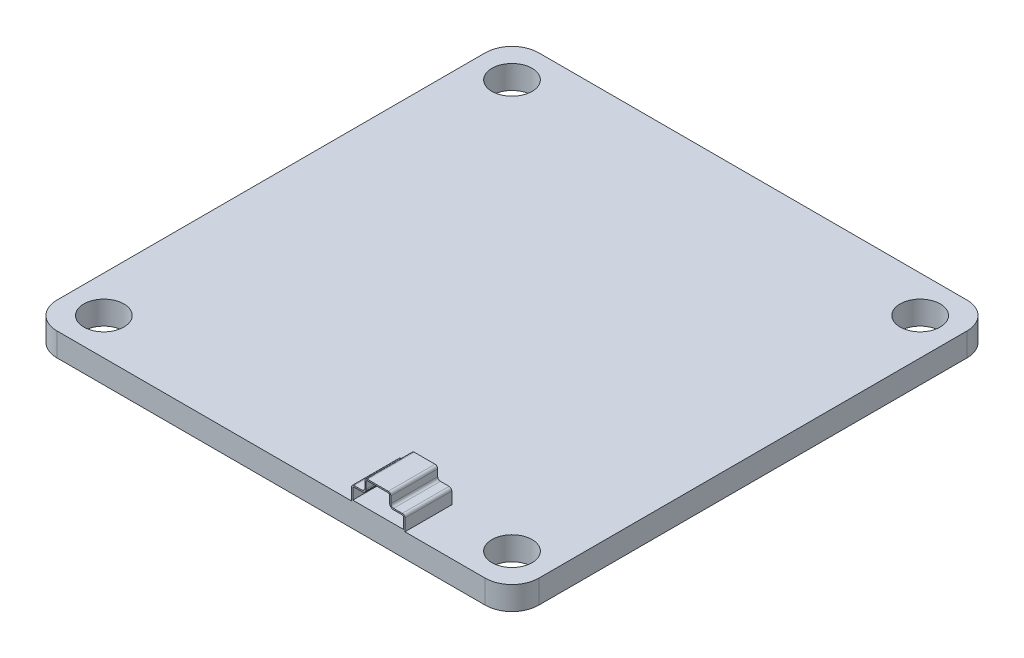
SolidWorks part; units mm, degrees
ref_plane "Front Plane" through (0, 0, 0) normal (0, 0, 1) x (1, 0, 0)
ref_plane "Top Plane" through (0, 0, 0) normal (0, 1, 0) x (1, 0, 0)
ref_plane "Right Plane" through (0, 0, 0) normal (1, 0, 0) x (0, 0, -1)
sketch "Sketch1" plane through (0, 0, 0) normal (0, 1, 0) x (1, 0, 0)
  line L1 (-16, 18) -> (16, 18)
  line L2 (-18, 16) -> (-18, -16)
  line L3 (-16, -18) -> (16, -18)
  line L4 (18, 16) -> (18, -16)
  line L5 (-18, 18) -> (18, -18) construction
  line L6 (-18, -18) -> (18, 18) construction
  line L7 (-15.25, 15.25) -> (15.25, 15.25) construction
  line L8 (-15.25, 15.25) -> (-15.25, -15.25) construction
  line L9 (-15.25, -15.25) -> (15.25, -15.25) construction
  line L10 (15.25, 15.25) -> (15.25, -15.25) construction
  line L11 (-15.25, 15.25) -> (15.25, -15.25) construction
  line L12 (-15.25, -15.25) -> (15.25, 15.25) construction
  circle A0 centre (-15.25, 15.25) radius 1.5
  circle A1 centre (15.25, 15.25) radius 1.5
  circle A2 centre (15.25, -15.25) radius 1.5
  circle A3 centre (-15.25, -15.25) radius 1.5
  arc A4 (-18, -16) -> (-16, -18) centre (-16, -16) ccw
  arc A5 (16, -18) -> (18, -16) centre (16, -16) ccw
  arc A6 (16, 18) -> (18, 16) centre (16, 16) cw
  arc A7 (-16, 18) -> (-18, 16) centre (-16, 16) ccw
  point P0 (0, 0)
  point P6 (0, 0)
  dimension "D3" = 3
  dimension "D4" = 2
  dimension "D1" = 36
  dimension "D2" = 30.5
extrude "Boss-Extrude2" add sketch "Sketch1" along normal blind 1.75
sketch "Sketch3" plane through (0, 0, 18) normal (0, 0, 1) x (1, 0, 0)
  line L0 (-16, 1.75) -> (16, 1.75) construction
  line L1 (6, 1.75) -> (10, 1.75)
  line L2 (6, 1.75) -> (6, 2.6439)
  line L3 (7.2024, 3.75) -> (8.7485, 3.75)
  line L4 (10, 1.75) -> (10, 2.6439)
  line L5 (16, 1.75) -> (16, 0) construction
  line L6 (7.0024, 3.55) -> (7.0024, 3.0439)
  line L7 (6.8024, 2.8439) -> (6.2, 2.8439)
  line L8 (8.9485, 3.55) -> (8.9485, 3.0439)
  line L9 (9.1485, 2.8439) -> (9.8, 2.8439)
  line L10 (6.1, 1.85) -> (6.1, 2.6439)
  line L11 (6.8024, 2.7439) -> (6.2, 2.7439)
  line L12 (7.1024, 3.55) -> (7.1024, 3.0439)
  line L13 (7.2024, 3.65) -> (8.7485, 3.65)
  line L14 (8.8485, 3.55) -> (8.8485, 3.0439)
  line L15 (9.1485, 2.7439) -> (9.8, 2.7439)
  line L16 (9.9, 1.85) -> (9.9, 2.6439)
  line L17 (6.1, 1.85) -> (9.9, 1.85)
  arc A0 (9.8, 2.8439) -> (10, 2.6439) centre (9.8, 2.6439) cw
  arc A1 (8.9485, 3.0439) -> (9.1485, 2.8439) centre (9.1485, 3.0439) ccw
  arc A2 (8.9485, 3.55) -> (8.7485, 3.75) centre (8.7485, 3.55) ccw
  arc A3 (7.0024, 3.55) -> (7.2024, 3.75) centre (7.2024, 3.55) cw
  arc A4 (7.0024, 3.0439) -> (6.8024, 2.8439) centre (6.8024, 3.0439) cw
  arc A5 (6.2, 2.8439) -> (6, 2.6439) centre (6.2, 2.6439) ccw
  arc A6 (6.2, 2.7439) -> (6.1, 2.6439) centre (6.2, 2.6439) ccw
  arc A7 (7.1024, 3.0439) -> (6.8024, 2.7439) centre (6.8024, 3.0439) cw
  arc A8 (7.1024, 3.55) -> (7.2024, 3.65) centre (7.2024, 3.55) cw
  arc A9 (8.8485, 3.55) -> (8.7485, 3.65) centre (8.7485, 3.55) ccw
  arc A10 (8.8485, 3.0439) -> (9.1485, 2.7439) centre (9.1485, 3.0439) ccw
  arc A11 (9.8, 2.7439) -> (9.9, 2.6439) centre (9.8, 2.6439) cw
  dimension "D1" = 0.2
  dimension "D2" = 0.1
  dimension "D3" = 6
extrude "Boss-Extrude3" add sketch "Sketch3" against normal blind 3
sketch "Sketch4" plane through (0, 0, 15) normal (0, 0, -1) x (-1, 0, 0)
  line L0 (-6, 1.75) -> (-10, 1.75) construction
  line L1 (-6, 2.6439) -> (-6, 1.75) construction
  line L2 (-6.8024, 2.8439) -> (-6.2, 2.8439) construction
  line L3 (-7.0024, 3.55) -> (-7.0024, 3.0439) construction
  line L4 (-8.7485, 3.75) -> (-7.2024, 3.75) construction
  line L5 (-8.9485, 3.0439) -> (-8.9485, 3.55) construction
  line L6 (-9.8, 2.8439) -> (-9.1485, 2.8439) construction
  line L7 (-10, 1.75) -> (-10, 2.6439) construction
  line L8 (-6, 1.75) -> (-10, 1.75)
  line L9 (-6, 2.6439) -> (-6, 1.75)
  line L10 (-6.8024, 2.8439) -> (-6.2, 2.8439)
  line L11 (-7.0024, 3.55) -> (-7.0024, 3.0439)
  line L12 (-8.7485, 3.75) -> (-7.2024, 3.75)
  line L13 (-8.9485, 3.0439) -> (-8.9485, 3.55)
  line L14 (-9.8, 2.8439) -> (-9.1485, 2.8439)
  line L15 (-10, 1.75) -> (-10, 2.6439)
  arc A0 (-6, 2.6439) -> (-6.2, 2.8439) centre (-6.2, 2.6439) ccw construction
  arc A1 (-7.0024, 3.0439) -> (-6.8024, 2.8439) centre (-6.8024, 3.0439) ccw construction
  arc A2 (-7.0024, 3.55) -> (-7.2024, 3.75) centre (-7.2024, 3.55) ccw construction
  arc A3 (-8.7485, 3.75) -> (-8.9485, 3.55) centre (-8.7485, 3.55) ccw construction
  arc A4 (-9.1485, 2.8439) -> (-8.9485, 3.0439) centre (-9.1485, 3.0439) ccw construction
  arc A5 (-9.8, 2.8439) -> (-10, 2.6439) centre (-9.8, 2.6439) ccw construction
  arc A6 (-6, 2.6439) -> (-6.2, 2.8439) centre (-6.2, 2.6439) ccw
  arc A7 (-7.0024, 3.0439) -> (-6.8024, 2.8439) centre (-6.8024, 3.0439) ccw
  arc A8 (-7.0024, 3.55) -> (-7.2024, 3.75) centre (-7.2024, 3.55) ccw
  arc A9 (-8.7485, 3.75) -> (-8.9485, 3.55) centre (-8.7485, 3.55) ccw
  arc A10 (-9.1485, 2.8439) -> (-8.9485, 3.0439) centre (-9.1485, 3.0439) ccw
  arc A11 (-9.8, 2.8439) -> (-10, 2.6439) centre (-9.8, 2.6439) ccw
extrude "Boss-Extrude4" add sketch "Sketch4" along normal blind 0.5
sketch "Sketch5" plane through (0, 0, 14.5) normal (0, 0, -1) x (-1, 0, 0)
  circle A0 centre (-8.5968, 2.5774) radius 0.2103
  circle A1 centre (-7.9292, 2.5774) radius 0.2103
  circle A2 centre (-7.3214, 2.5774) radius 0.2103
  point P6 (-8.8815, 2.5774)
  point P7 (-7.2221, 2.5774)
  point P8 (-7.9292, 2.5774)
  point P9 (-8.5968, 2.5774)
  point P10 (-7.3214, 2.5774)
  point P11 (0, 0)
extrude "Cut-Extrude1" cut sketch "Sketch5" against normal blind 0.5
